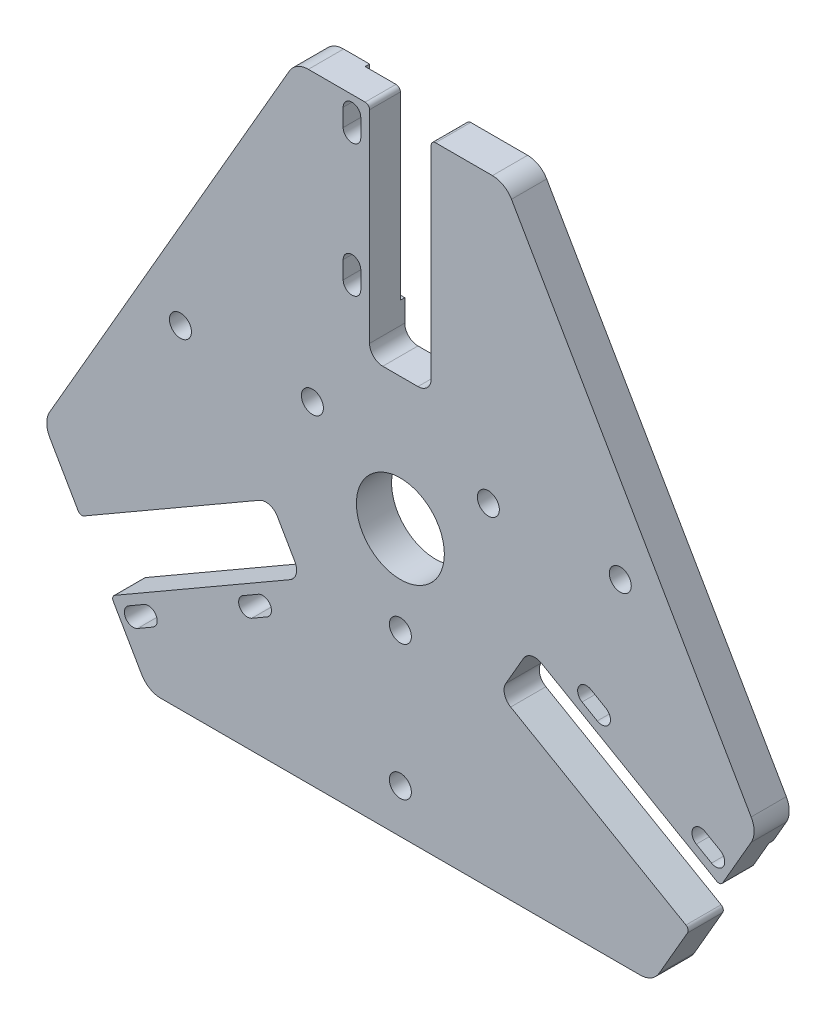
SolidWorks part; units mm, degrees
ref_plane "Front Plane" through (0, 0, 0) normal (0, 0, 1) x (1, 0, 0)
ref_plane "Top Plane" through (0, 0, 0) normal (0, 1, 0) x (1, 0, 0)
ref_plane "Right Plane" through (0, 0, 0) normal (1, 0, 0) x (0, 0, -1)
sketch "Sketch3" plane through (0, 0, 0) normal (0, 0, 1) x (1, 0, 0)
  line L0 (0, 0) -> (0, 80)
  line L4 (-25.2554, 77.5) -> (-79.7446, -16.8782)
  line L5 (-54.4893, -60.6218) -> (54.4893, -60.6218)
  line L6 (79.7446, -16.8782) -> (25.2554, 77.5)
  line L7 (20.9252, 80) -> (-20.9252, 80)
  line L9 (-79.7446, -21.8782) -> (-58.8194, -58.1218)
  line L10 (79.7446, -21.8782) -> (58.8194, -58.1218)
  line L11 (0, 0) -> (-69.282, -40)
  line L12 (0, 0) -> (69.282, -40)
  arc A0 (-79.7446, -21.8782) -> (-79.7446, -16.8782) centre (-75.4145, -19.3782) cw
  arc A1 (-54.4893, -60.6218) -> (-58.8194, -58.1218) centre (-54.4893, -55.6218) cw
  arc A2 (58.8194, -58.1218) -> (54.4893, -60.6218) centre (54.4893, -55.6218) cw
  arc A3 (79.7446, -21.8782) -> (79.7446, -16.8782) centre (75.4145, -19.3782) ccw
  arc A4 (20.9252, 80) -> (25.2554, 77.5) centre (20.9252, 75) cw
  arc A5 (-20.9252, 80) -> (-25.2554, 77.5) centre (-20.9252, 75) ccw
  point P4 (-81.188, -19.3782)
  point P8 (-81.188, -19.3782)
  point P11 (-57.376, -60.6218)
  point P12 (81.188, -19.3782)
  point P13 (57.376, -60.6218)
  point P20 (-57.376, -60.6218)
  point P23 (57.376, -60.6218)
  point P26 (81.188, -19.3782)
  dimension "D1" = 5
  dimension "D3" = 5
  dimension "D2" = 80
extrude "Boss-Extrude1" add sketch "Sketch3" along normal blind 8 contours A2 L10 L12 L11 L9 A1 L5 | A4 L7 L0 L12 L10 A3 L6 | L7 A5 L4 A0 L9 L11 L0
sketch "Sketch5" plane through (0, 0, 8) normal (0, 0, 1) x (1, 0, 0)
  line L0 (-7.0091, 80) -> (-7.0091, 32.9937)
  line L1 (-4.0091, 29.9937) -> (3.9909, 29.9937)
  line L2 (6.9909, 80) -> (6.9909, 32.9937)
  line L3 (-72.7816, -33.9386) -> (-32.088, -10.4441)
  line L4 (72.777, -33.9465) -> (32.0697, -10.4441)
  line L5 (-27.9899, -11.5422) -> (-23.9899, -18.4704)
  line L6 (27.9716, -11.5422) -> (23.9716, -18.4704)
  line L7 (-65.7816, -46.063) -> (-25.088, -22.5685)
  line L8 (65.777, -46.0709) -> (25.0697, -22.5685)
  line L9 (-11.0091, 76.4937) -> (-11.0091, 72.4937) construction
  line L10 (-9.0091, 76.4937) -> (-9.0091, 72.4937)
  line L11 (-13.0091, 76.4937) -> (-13.0091, 72.4937)
  line L12 (-11.0091, 46.4937) -> (-11.0091, 42.4937) construction
  line L13 (-9.0091, 46.4937) -> (-9.0091, 42.4937)
  line L14 (-13.0091, 46.4937) -> (-13.0091, 42.4937)
  line L15 (-62.1551, -48.588) -> (-54.4964, -44.1663) construction
  line L16 (-60.7601, -47.7826) -> (-57.296, -45.7826) construction
  line L17 (-61.7601, -46.0506) -> (-58.296, -44.0506)
  line L18 (-59.7601, -49.5147) -> (-56.296, -47.5147)
  line L19 (-34.7793, -32.7826) -> (-31.3152, -30.7826) construction
  line L20 (-35.7793, -31.0506) -> (-32.3152, -29.0506)
  line L21 (-33.7793, -34.5147) -> (-30.3152, -32.5147)
  line L22 (65.0218, -24.8503) -> (74.846, -30.5223) construction
  line L23 (68.2777, -26.73) -> (71.7418, -28.73) construction
  line L24 (69.2777, -24.998) -> (72.7418, -26.998)
  line L25 (67.2777, -28.4621) -> (70.7418, -30.4621)
  line L26 (42.2969, -11.73) -> (45.761, -13.73) construction
  line L27 (43.2969, -9.998) -> (46.761, -11.998)
  line L28 (41.2969, -13.4621) -> (44.761, -15.4621)
  line L29 (20.9252, 80) -> (-20.9252, 80) construction
  line L30 (79.7446, -21.8782) -> (58.8194, -58.1218) construction
  line L31 (-79.7446, -21.8782) -> (-58.8194, -58.1218) construction
  circle A0 centre (-0.0091, -0.0063) radius 10
  circle A1 centre (-0.0091, -20.0063) radius 2.5
  circle A2 centre (-0.0091, -50.6281) radius 2.5
  arc A3 (3.9909, 29.9937) -> (6.9909, 32.9937) centre (3.9909, 32.9937) ccw
  arc A4 (-4.0091, 29.9937) -> (-7.0091, 32.9937) centre (-4.0091, 32.9937) cw
  arc A5 (27.9716, -11.5422) -> (32.0697, -10.4441) centre (30.5697, -13.0422) cw
  arc A6 (23.9716, -18.4704) -> (25.0697, -22.5685) centre (26.5697, -19.9704) ccw
  arc A7 (-23.9899, -18.4704) -> (-25.088, -22.5685) centre (-26.588, -19.9704) cw
  arc A8 (-27.9899, -11.5422) -> (-32.088, -10.4441) centre (-30.588, -13.0422) ccw
  circle A9 centre (-20.0091, 14.9937) radius 2.5
  circle A10 centre (-50.0091, 14.9937) radius 2.5
  circle A11 centre (19.9909, 14.9937) radius 2.5
  circle A12 centre (49.9909, 14.9937) radius 2.5
  arc A13 (-9.0091, 76.4937) -> (-13.0091, 76.4937) centre (-11.0091, 76.4937) ccw
  arc A14 (-13.0091, 72.4937) -> (-9.0091, 72.4937) centre (-11.0091, 72.4937) ccw
  arc A15 (-9.0091, 46.4937) -> (-13.0091, 46.4937) centre (-11.0091, 46.4937) ccw
  arc A16 (-13.0091, 42.4937) -> (-9.0091, 42.4937) centre (-11.0091, 42.4937) ccw
  arc A17 (-61.7601, -46.0506) -> (-59.7601, -49.5147) centre (-60.7601, -47.7826) ccw
  arc A18 (-56.296, -47.5147) -> (-58.296, -44.0506) centre (-57.296, -45.7826) ccw
  arc A19 (-35.7793, -31.0506) -> (-33.7793, -34.5147) centre (-34.7793, -32.7826) ccw
  arc A20 (-30.3152, -32.5147) -> (-32.3152, -29.0506) centre (-31.3152, -30.7826) ccw
  arc A21 (69.2777, -24.998) -> (67.2777, -28.4621) centre (68.2777, -26.73) ccw
  arc A22 (70.7418, -30.4621) -> (72.7418, -26.998) centre (71.7418, -28.73) ccw
  arc A23 (43.2969, -9.998) -> (41.2969, -13.4621) centre (42.2969, -11.73) ccw
  arc A24 (44.761, -15.4621) -> (46.761, -11.998) centre (45.761, -13.73) ccw
  point P10 (-0.0091, 29.9937)
  point P21 (-25.9899, -15.0063)
  point P24 (25.9716, -15.0063)
  point P43 (-11.0091, 74.4937)
  point P51 (-11.0091, 44.4937)
  point P59 (-59.028, -46.7826)
  point P68 (-33.0473, -31.7826)
  point P75 (70.0098, -27.73)
  point P82 (44.029, -12.73)
  line M8 (20.9252, 80) -> (-20.9252, 80)
  line M12 (-79.7446, -21.8782) -> (-58.8194, -58.1218)
  line M16 (58.8194, -58.1218) -> (79.7446, -21.8782)
  dimension "D1" = 20
  dimension "D2" = 5
  dimension "D3" = 5
  dimension "D5" = 3
  dimension "D6" = 3
  dimension "D9" = 5
  dimension "D11" = 2
  dimension "D14" = 2
  dimension "D17" = 2
  dimension "D4" = 20
  dimension "D7" = 13
  dimension "D8" = 15
  dimension "D10" = 4
  dimension "D12" = 2
  dimension "D13" = 4
  dimension "D15" = 2
  dimension "D16" = 4
  dimension "D18" = 2
extrude "Cut-Extrude26" cut sketch "Sketch5" against normal through all contours A4 L1 A3 L2 L0 M8 | L11 A14 L10 A13 | L14 A16 L13 A15 | A12 | A11 | A9 | A10 | A0 | L5 A8 L3 L7 A7 M12 | L21 A20 L20 A19 | L18 A18 L17 A17 | A2 | A1 | L6 A6 L8 L4 A5 M16 | L28 A24 L27 A23 | L25 A22 L24 A21
fillet "Fillet2" radius 1 1 edges at (72.777, -33.9465, 4)
fillet "Fillet3" radius 1 5 edges at (6.9909, 80, 4) (-7.0091, 80, 4) (-65.7816, -46.063, 4) (-72.7816, -33.9386, 4) (65.777, -46.0709, 4)
sketch "Sketch7" plane through (0, 0, 0) normal (0, 0, -1) x (-1, 0, 0)
  line L4 (61.7816, -52.9912) -> (30.6047, -34.9912)
  line L5 (-76.777, -27.0183) -> (-45.6001, -9.0183)
  line L6 (-47.4931, -14.73) -> (-40.5649, -10.73) construction
  line L7 (-40.5649, -10.73) -> (-44.2422, -4.3608) construction
  line L8 (-76.777, -27.0183) -> (-72.777, -33.9465)
  line L9 (-38.9039, -8.6164) -> (-36.4039, -12.9465)
  line L10 (-72.777, -33.9465) -> (-36.4039, -12.9465)
  line L11 (-79.7446, -21.8782) -> (-73.277, -33.0805) construction
  line L12 (61.7816, -52.9912) -> (65.7816, -46.063)
  line L13 (-71.911, -33.4465) -> (-32.0697, -10.4441) construction
  line L14 (26.9085, -29.3931) -> (29.4085, -25.063)
  line L15 (65.7816, -46.063) -> (29.4085, -25.063)
  line L16 (65.2816, -46.929) -> (58.8194, -58.1218) construction
  line L18 (64.9156, -45.563) -> (25.088, -22.5685) construction
  line L19 (36.5114, -33.7826) -> (29.5832, -29.7826) construction
  line L20 (15.0091, 80) -> (15.0091, 44)
  line L21 (15.0091, 80) -> (7.0091, 80)
  line L22 (12.0091, 38) -> (7.0091, 38)
  line L23 (7.0091, 80) -> (7.0091, 38)
  line L24 (8.0091, 80) -> (20.9252, 80) construction
  line L26 (7.0091, 79) -> (7.0091, 32.9937) construction
  arc A0 (-46.761, -11.998) -> (-44.761, -15.4621) centre (-45.761, -13.73) ccw construction
  arc A1 (-41.2969, -13.4621) -> (-43.2969, -9.998) centre (-42.2969, -11.73) ccw construction
  arc A2 (-38.9039, -8.6164) -> (-45.6001, -9.0183) centre (-42.3525, -7.1433) ccw
  arc A3 (33.7793, -34.5147) -> (35.7793, -31.0506) centre (34.7793, -32.7826) ccw construction
  arc A4 (32.3152, -29.0506) -> (30.3152, -32.5147) centre (31.3152, -30.7826) ccw construction
  arc A5 (26.9085, -29.3931) -> (30.6047, -34.9912) centre (27.3571, -33.1162) ccw
  arc A6 (12.0091, 38) -> (15.0091, 44) centre (15.0091, 40.25) ccw
  point P14 (-44.029, -12.73)
  point P20 (-38.9039, -8.6164)
  point P21 (-45.6001, -9.0183)
  point P40 (26.9085, -29.3931)
  point P41 (30.6047, -34.9912)
  point P52 (15.0091, 44)
  point P53 (12.0091, 38)
  dimension "D1" = 8
  dimension "D3" = 5
  dimension "D4" = 36
  dimension "D7" = 5
  dimension "D8" = 36
  dimension "D11" = 36
  dimension "D12" = 5
extrude "Cut-Extrude27" cut sketch "Sketch7" against normal blind 1 contours L9 L10 L8 L5 A2 | A5 L4 L12 L15 L14 | L20 A6 L22 L23 L21
fillet "Fillet4" radius 1 3 edges at (45.6001, -9.0183, 0.5) (-30.6047, -34.9912, 0.5) (-15.0091, 44, 0.5)
